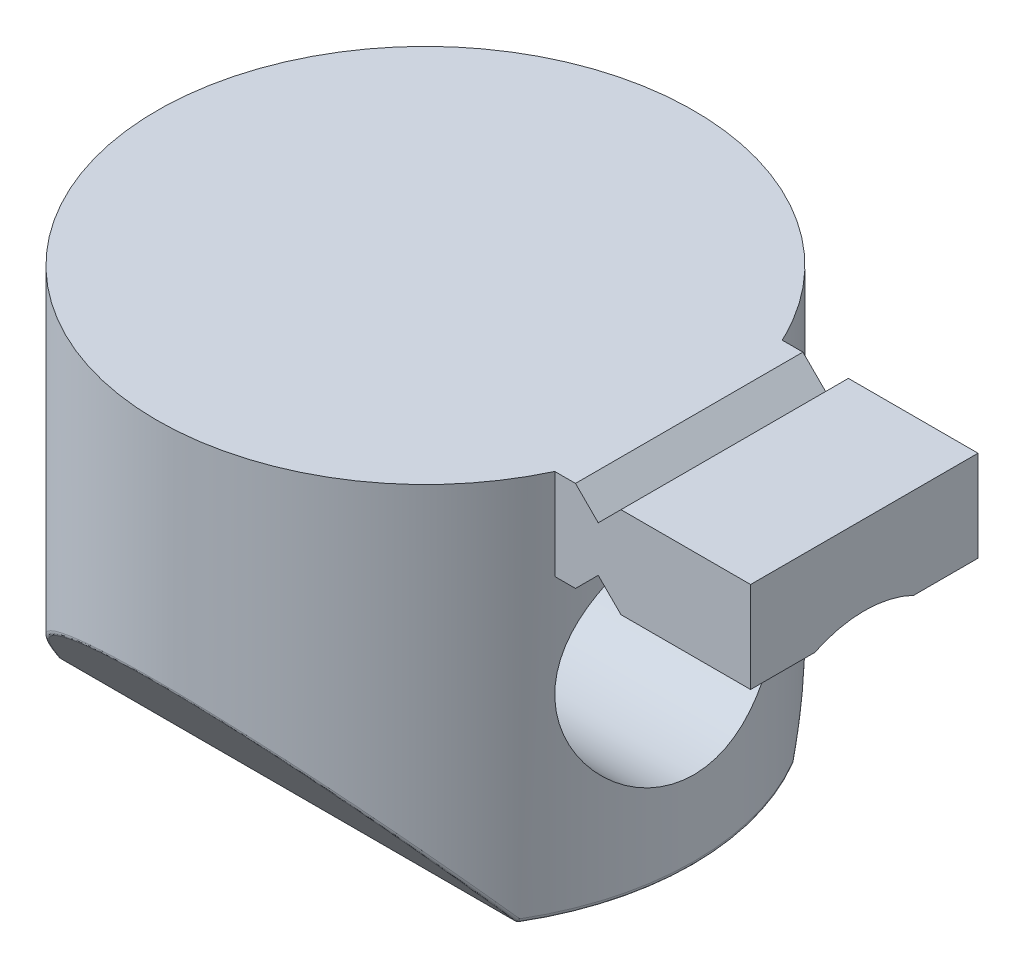
SolidWorks part; units mm, degrees
material "Zinc AG40A (Zn-4Al-0.4Mg; Zamak 3), Cast"
ref_plane "Front Plane" through (0, 0, 0) normal (0, 0, 1) x (1, 0, 0)
ref_plane "Top Plane" through (0, 0, 0) normal (0, 1, 0) x (1, 0, 0)
ref_plane "Right Plane" through (0, 0, 0) normal (1, 0, 0) x (0, 0, -1)
sketch "Sketch1" plane through (0, 0, 0) normal (0, 1, 0) x (1, 0, 0)
  circle A0 centre (0, 0) radius 5.9
extrude "Extrude1" add sketch "Sketch1" along normal blind 8.5
sketch "Sketch2" plane through (0, 8.5, 0) normal (0, 1, 0) x (1, 0, 0)
  line L0 (0, 2.5) -> (0, -2.5)
  line L1 (0, 2.5) -> (9.65, 2.5)
  line L2 (0, -2.5) -> (9.65, -2.5)
  line L3 (9.65, -2.5) -> (9.65, 2.5)
extrude "Extrude2" add sketch "Sketch2" against normal blind 2
sketch "Sketch3" plane through (9.65, 0, 0) normal (1, 0, 0) x (0, 0, -1)
  circle A0 centre (0, 4.25) radius 2.5
extrude "Cut-Extrude1" cut sketch "Sketch3" against normal through all
sketch "Sketch4" plane through (0, 0, 2.5) normal (0, 0, 1) x (1, 0, 0)
  line L2 (6.8, 8.5) -> (5.8, 8.5)
  line L3 (6.3, 7) -> (5.8, 6.5)
  line L4 (6.8, 6.5) -> (6.3, 7)
  line L5 (6.8, 6.5) -> (5.8, 6.5)
  line L8 (6.8, 8.5) -> (6.3, 8)
  line L9 (6.3, 8) -> (5.8, 8.5)
extrude "Cut-Extrude2" cut sketch "Sketch4" against normal through all
sketch "Sketch5" plane through (9.65, 0, 0) normal (1, 0, 0) x (0, 0, -1)
  line L0 (-5.9, 3.5) -> (-6.1063, 3.5)
  line L1 (-6.1063, 3.5) -> (-6.0031, -0.2786)
  line L2 (-6.0031, -0.2786) -> (6.1063, -0.1561)
  line L4 (3, 0) -> (5.9, 3.5)
  line L5 (6.1063, -0.1561) -> (6.1063, 3.6322)
  line L6 (6.1063, 3.6322) -> (5.9, 3.5)
  line L7 (-3, 0) -> (-5.9, 3.5)
  line L8 (3, 0) -> (-3, 0)
extrude "Cut-Extrude3" cut sketch "Sketch5" against normal through all
fillet "Fillet2" radius 0.1 6 edges at (0, 3.5, -5.9) (0, 0, -3) (-5.9, 0, 0) (5.9, 0, 0) (0, 3.5, 5.9) (0, 0, 3)
ref_plane "Plane1" through (-5.9, 0, 0) normal (1, 0, 0) x (0, 0, -1)
sketch "Sketch7" plane through (-5.9, 0, 0) normal (1, 0, 0) x (0, 0, -1)
  line L0 (-4, 4.25) -> (-2, 7.7141)
  line L1 (-2, 7.7141) -> (2, 7.7141)
  line L2 (2, 7.7141) -> (4, 4.25)
  line L3 (4, 4.25) -> (2, 0.7859)
  line L4 (2, 0.7859) -> (-2, 0.7859)
  line L5 (-2, 0.7859) -> (-4, 4.25)
extrude "Cut-Extrude5" cut sketch "Sketch7" along normal blind 7
